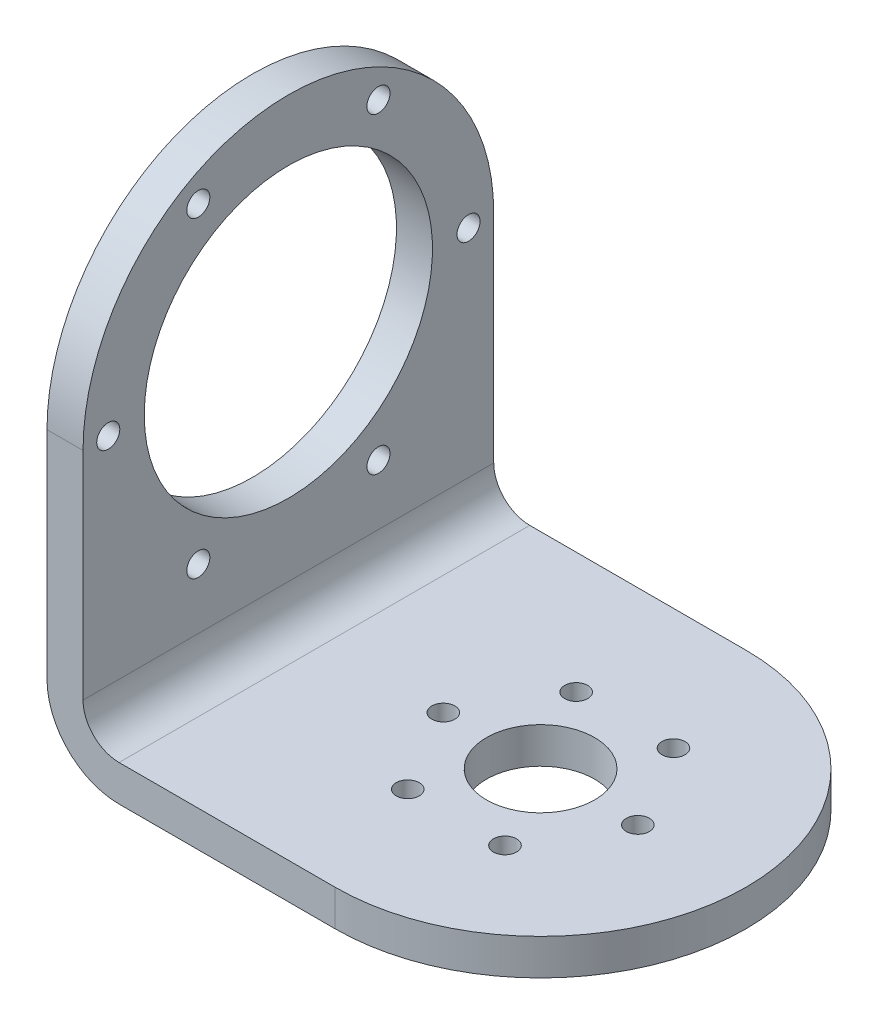
SolidWorks part; units mm, degrees
material "AISI 304"
ref_plane "前视基准面" through (0, 0, 0) normal (0, 0, 1) x (1, 0, 0)
ref_plane "上视基准面" through (0, 0, 0) normal (0, 1, 0) x (1, 0, 0)
ref_plane "右视基准面" through (0, 0, 0) normal (1, 0, 0) x (0, 0, -1)
sketch "草图1" plane through (0, 0, 0) normal (0, 1, 0) x (1, 0, 0)
  line L0 (0, 28.5) -> (-40, 28.5)
  line L1 (-40, 28.5) -> (-40, -28.5)
  line L2 (-40, -28.5) -> (0, -28.5)
  line L3 (-35, 28.5) -> (-35, -28.5)
  circle A0 centre (0, 0) radius 28.5
  dimension "D1" = 57
  dimension "D2" = 40
  dimension "D3" = 5
extrude "凸台-拉伸1" add sketch "草图1" along normal blind 5 contours A0 L0 L3 L2 | A0 | L3 L0 L1 L2
sketch "草图2" plane through (-40, 0, 0) normal (-1, 0, 0) x (0, 0, 1)
  line L0 (-28.5, 40) -> (-28.5, 0)
  line L1 (-28.5, 0) -> (28.5, 0)
  line L2 (28.5, 0) -> (28.5, 40)
  line L3 (0, 65) -> (0, 40) construction
  line L4 (-12.5, 61.6506) -> (0, 40) construction
  circle A0 centre (0, 40) radius 28.5
  circle A1 centre (0, 40) radius 20
  circle A2 centre (0, 40) radius 25 construction
  circle A9 centre (-12.5, 61.6506) radius 1.6
  circle A10 centre (12.5, 61.6506) radius 1.6
  circle A11 centre (25, 40) radius 1.6
  circle A12 centre (12.5, 18.3494) radius 1.6
  circle A13 centre (-12.5, 18.3494) radius 1.6
  circle A14 centre (-25, 40) radius 1.6
  point P25 (0, 40)
  point P26 (0, 40)
  line M6 (28.5, 5) -> (-28.5, 5)
  dimension "D1" = 57
  dimension "D3" = 40
  dimension "D4" = 50
  dimension "D5" = 30
  dimension "D6" = 3.2
  dimension "D2" = 40
  dimension "D7" = 6
extrude "凸台-拉伸2" add sketch "草图2" against normal blind 5 contours A0 L0 L2 M6 | A0 A14 A2 A9 A10 A11 A12 A13 | A14 A2 A13 A12 A11 A10 A9 A1
fillet "圆角1" radius 10 1 edges at (-40, 0, 0)
fillet "圆角2" radius 5 1 edges at (-35, 5, 0)
sketch "草图3" plane through (0, 5, 0) normal (0, 1, 0) x (1, 0, 0)
  circle A0 centre (0, 0) radius 13.5 construction
  circle A1 centre (13.5, 0) radius 1.6
  circle A2 centre (6.75, -11.6913) radius 1.6
  circle A3 centre (-6.75, -11.6913) radius 1.6
  circle A4 centre (-13.5, 0) radius 1.6
  circle A5 centre (-6.75, 11.6913) radius 1.6
  circle A6 centre (6.75, 11.6913) radius 1.6
  circle A7 centre (0, 0) radius 7.5
  point P17 (0, 0)
  dimension "D1" = 27
  dimension "D2" = 3.2
  dimension "D4" = 15
  dimension "D3" = 6
extrude "切除-拉伸1" cut sketch "草图3" against normal blind 5
sketch "草图4" plane through (0, 0, 0) normal (0, -1, 0) x (1, 0, 0)
  circle A0 centre (0, 0) radius 22.5
  circle A1 centre (0, 22.5) radius 1.5
  circle A2 centre (0, -22.5) radius 1.5
  circle A7 centre (-35, -22.5) radius 1.5
  circle A8 centre (-35, 22.5) radius 1.5
  circle A9 centre (-70, -22.5) radius 1.5
  circle A10 centre (-70, 22.5) radius 1.5
  dimension "D1" = 45
  dimension "D2" = 3
  dimension "D3" = 3
  dimension "D4" = 3
